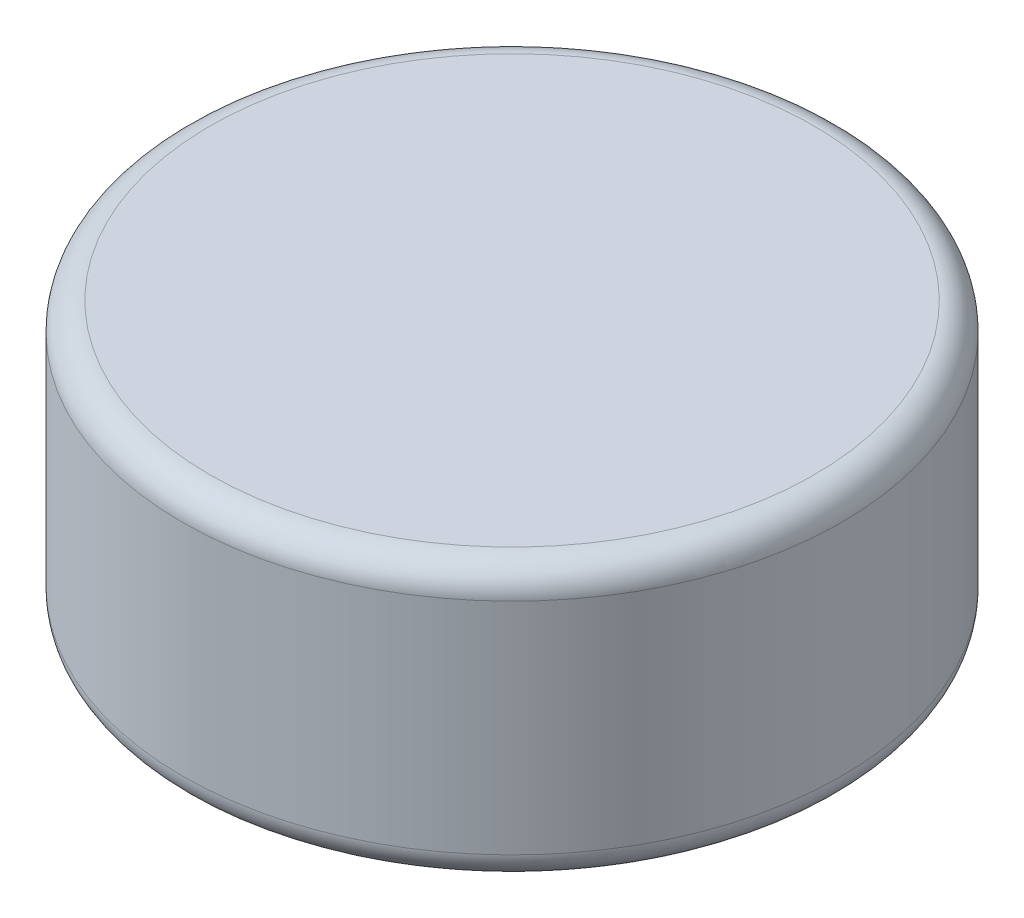
SolidWorks part; units mm, degrees
ref_plane "Front Plane" through (0, 0, 0) normal (0, 0, 1) x (1, 0, 0)
ref_plane "Top Plane" through (0, 0, 0) normal (0, 1, 0) x (1, 0, 0)
ref_plane "Right Plane" through (0, 0, 0) normal (1, 0, 0) x (0, 0, -1)
sketch "Sketch1" plane through (0, 0, 0) normal (0, 1, 0) x (1, 0, 0)
  circle A0 centre (0, 0) radius 3
  dimension "D1" = 6
extrude "Boss-Extrude1" add sketch "Sketch1" along normal mid plane 2.5
fillet "Fillet1" radius 0.25 2 edges at (0, -1.25, 3) (0, 1.25, 3)
